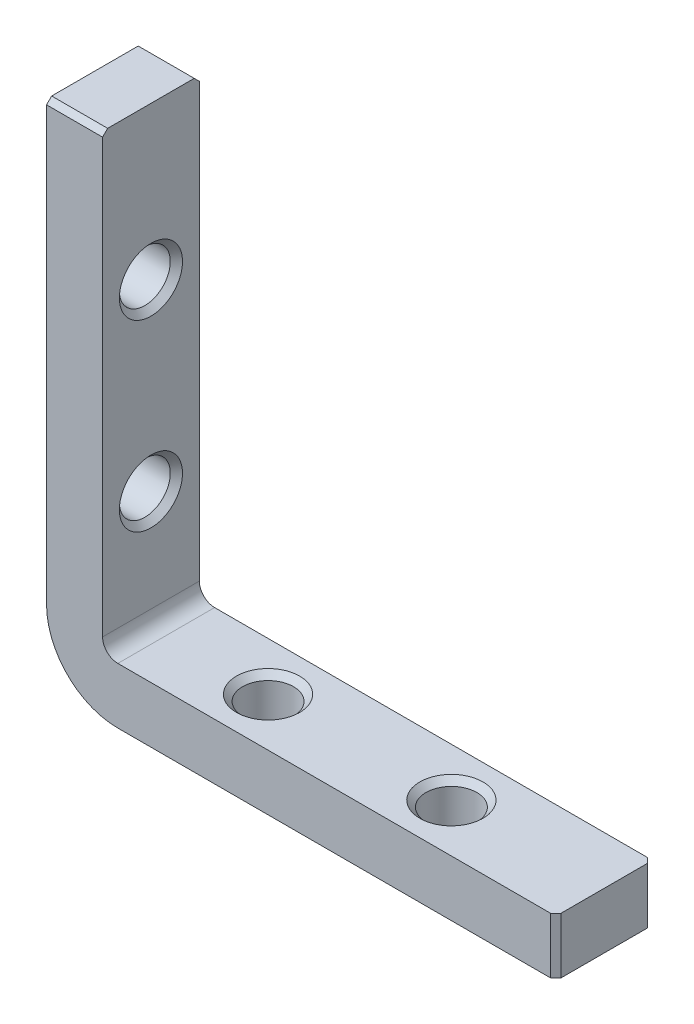
SolidWorks part; units mm, degrees
material "Сталь 20  ГОСТ 1050-2013"
ref_plane "Спереди" through (0, 0, 0) normal (0, 0, 1) x (1, 0, 0)
ref_plane "Сверху" through (0, 0, 0) normal (0, 1, 0) x (1, 0, 0)
ref_plane "Справа" through (0, 0, 0) normal (1, 0, 0) x (0, 0, -1)
sketch "Эскиз1" plane through (0, 0, 0) normal (0, 0, 1) x (1, 0, 0)
  line L0 (0, 50) -> (0, 7)
  line L1 (7, 0) -> (50, 0)
  line L2 (50, 5.5) -> (7, 5.5)
  line L3 (5.5, 7) -> (5.5, 50)
  line L8 (50, 5.5) -> (50, 0)
  line L9 (5.5, 50) -> (0, 50)
  arc A4 (0, 7) -> (7, 0) centre (7, 7) ccw
  arc A5 (7, 5.5) -> (5.5, 7) centre (7, 7) cw
  point P9 (0, 0)
  point P12 (0, 0)
  point P13 (5.5, 7)
  dimension "D3" = 7
  dimension "D1" = 50
  dimension "D2" = 5.5
extrude "Бобышка-Вытянуть1" add sketch "Эскиз1" along normal mid plane 9.5
hole_wizard "Отверстие обработанное метчиком M61" positions "Эскиз4" profile "Эскиз5" tap size "M6" standard "ISO" end condition through all
sketch "Эскиз4" plane through (0, 0, 0) normal (-1, 0, 0) x (0, 0, 1)
  line L9 (4.75, 50) -> (-4.75, 50) construction
  point P0 (0, 35)
  point P2 (0, 17)
  dimension "D1" = 15
  dimension "D2" = 18
sketch "Эскиз5" plane through (0, 35, 0) normal (0, 1, 0) x (0, 0, 1)
  line L0 (0, 0) -> (0, 5.5)
  line L1 (0, 5.5) -> (3.1, 5.5)
  line L2 (2.5, 4.9) -> (2.5, 0.6)
  line L3 (2.5, 0.6) -> (3.1, 0)
  line L5 (3.1, 0) -> (0, 0)
  line L6 (-2.5, 0.6) -> (-3.1, 0) construction
  line L7 (3.1, 5.5) -> (2.5, 4.9)
  line L8 (-3.1, 5.5) -> (-2.5, 4.9) construction
  line L11 (0, -6.35) -> (0, 107.95) construction
  dimension "Диаметр проходного сверла" = 5
  dimension "Глубина проходного сверла" = 5.5
  dimension "Диаметр передней зенковки" = 6.2
  dimension "Угол передней зенковки" = 90
  dimension "Диаметр задней зенковки" = 6.2
  dimension "Угол задней зенковки" = 90
cosmetic thread "Отверстие резьбы1" parameters "D2"=6
cosmetic thread "Отверстие резьбы2" parameters "D2"=6
ref_plane "Плоскость1" through (0, 0, 0) normal (-0.7071, 0.7071, 0) x (0.7071, 0.7071, 0)
mirror "Зеркальное отражение1" about plane through (0, 0, 0) normal (-0.7071, 0.7071, 0) of "Отверстие обработанное метчиком M61"
chamfer "Фаска1" distance 0.5 angle 45 4 edges at (50, 2.75, -4.75) (50, 2.75, 4.75) (2.75, 50, -4.75) (2.75, 50, 4.75)
